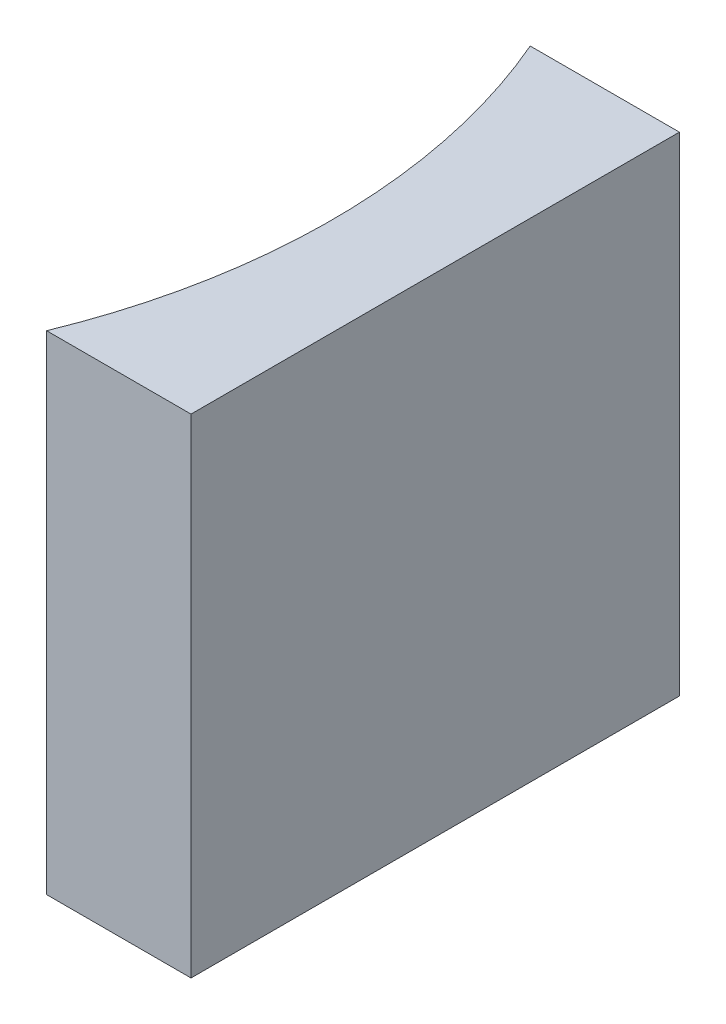
SolidWorks part; units mm, degrees
ref_plane "前视基准面" through (0, 0, 0) normal (0, 0, 1) x (1, 0, 0)
ref_plane "上视基准面" through (0, 0, 0) normal (0, 1, 0) x (1, 0, 0)
ref_plane "右视基准面" through (0, 0, 0) normal (1, 0, 0) x (0, 0, -1)
sketch "草图1" plane through (0, 0, 0) normal (0, 1, 0) x (1, 0, 0)
  line L0 (0, 0) -> (0, -10)
  line L1 (0, 0) -> (-3.0548, 0)
  line L2 (0, -10) -> (-2.957, -10)
  line L3 (2.8382, -5.1166) -> (-15.8359, -5.1166) construction
  arc A0 (-2.957, -10) -> (-3.0548, 0) centre (-14.9294, -5.1166) ccw
  point P7 (-2, -4.9902)
  point P8 (0, -5)
  point P10 (2.8382, -5.1166)
  dimension "D2" = 12.93
  dimension "D3" = 2
  dimension "D4" = 3.0548
  dimension "D1" = 10
extrude "凸台-拉伸1" add sketch "草图1" along normal blind 10
